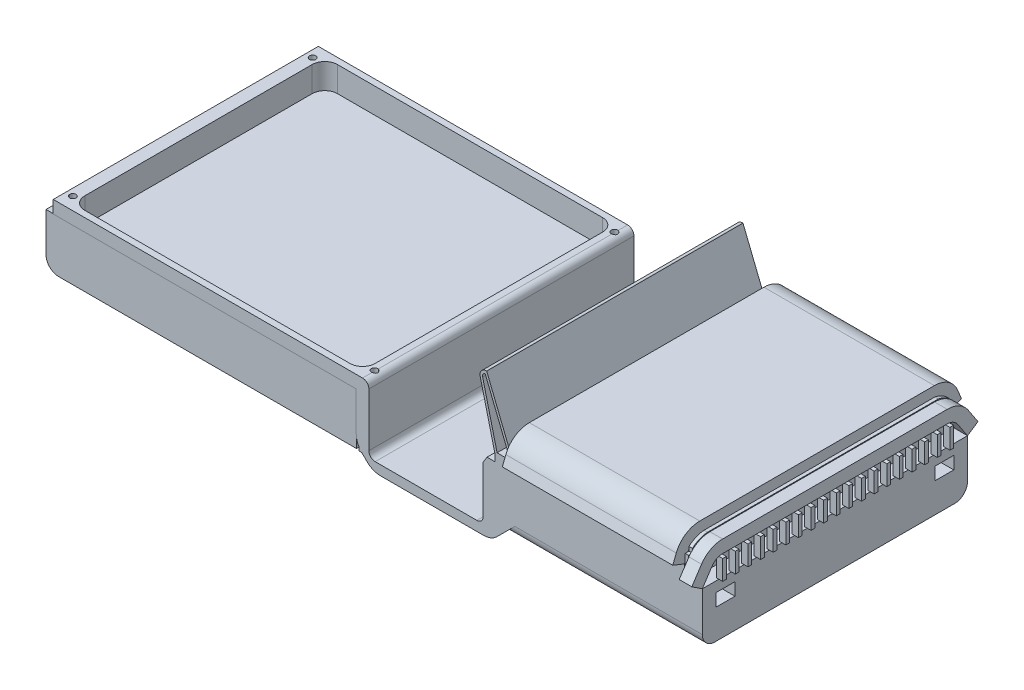
SolidWorks part; units mm, degrees
ref_plane "Front Plane" through (0, 0, 0) normal (0, 0, 1) x (1, 0, 0)
ref_plane "Top Plane" through (0, 0, 0) normal (0, 1, 0) x (1, 0, 0)
ref_plane "Right Plane" through (0, 0, 0) normal (1, 0, 0) x (0, 0, -1)
sketch "Sketch1" plane through (0, 0, 0) normal (0, 0, 1) x (1, 0, 0)
  line L0 (-144.6727, 0) -> (257.8658, 0) construction
  line L1 (-242.1342, 0) -> (7.8658, 0)
  line L2 (7.8658, 0) -> (7.8658, -40.8579)
  line L3 (9.3302, -44.3934) -> (13.4724, -48.5355)
  line L4 (17.0079, -50) -> (98.7236, -50)
  line L5 (102.2592, -48.5355) -> (106.4013, -44.3934)
  line L6 (107.8658, -40.8579) -> (107.8658, 0)
  line L7 (107.8658, 0) -> (257.8658, 0)
  arc A0 (106.4013, -44.3934) -> (107.8658, -40.8579) centre (102.8658, -40.8579) ccw
  arc A1 (98.7236, -50) -> (102.2592, -48.5355) centre (98.7236, -45) ccw
  arc A2 (13.4724, -48.5355) -> (17.0079, -50) centre (17.0079, -45) ccw
  arc A3 (7.8658, -40.8579) -> (9.3302, -44.3934) centre (12.8658, -40.8579) ccw
  point P5 (121.9448, 0)
  point P12 (-135.7907, 0)
  point P13 (158.4975, 0)
  point P16 (107.8658, -42.9289)
  point P19 (100.7947, -50)
  point P22 (14.9368, -50)
  point P25 (7.8658, -42.9289)
  dimension "D7" = 5
  dimension "D1" = 250
  dimension "D2" = 100
  dimension "D3" = 150
  dimension "D4" = 50
  dimension "D5" = 10
  dimension "D6" = 10
extrude "Extrude-Thin1" add sketch "Sketch1" against normal mid plane 210 thin
sketch "Sketch3" plane through (257.8658, 0, 0) normal (1, 0, 0) x (0, 0, -1)
  line L0 (-105, 0) -> (-102.2142, 7.0316)
  line L1 (-92.9172, 13.3483) -> (92.9172, 13.3483)
  line L2 (0, -17.7197) -> (0, 27.8327) construction
  line L3 (105, 0) -> (102.2142, 7.0316)
  arc A0 (-102.2142, 7.0316) -> (-92.9172, 13.3483) centre (-92.9172, 3.3483) cw
  arc A1 (102.2142, 7.0316) -> (92.9172, 13.3483) centre (92.9172, 3.3483) ccw
  point P13 (0, 13.3483)
  dimension "D1" = 10
extrude "Extrude-Thin2" add sketch "Sketch3" against normal blind 135 separate body thin thin type one direction wall 10
sketch "Sketch4" plane through (0, 0, 0) normal (1, 0, 0) x (0, 0, -1)
  line L0 (105, -51.4645) -> (105, -40.8579) construction
  line L1 (-105, -10) -> (105, -10)
  line L2 (-105, -10) -> (-105, -51.4645)
  line L3 (-105, -51.4645) -> (105, -51.4645)
  line L4 (105, -10) -> (105, -51.4645)
extrude "Boss-Extrude1" add sketch "Sketch4" along normal blind 272
sketch "Sketch5" plane through (0, 0, 105) normal (0, 0, 1) x (1, 0, 0)
  line L1 (7.8658, -10) -> (107.309, -10)
  line L2 (7.8658, -10) -> (7.8658, -52.3732)
  line L3 (7.8658, -52.3732) -> (107.309, -52.3732)
  line L4 (107.309, -10) -> (107.309, -52.3732)
extrude "Cut-Extrude1" cut sketch "Sketch5" against normal blind 709
sketch "Sketch6" plane through (272, 0, 0) normal (1, 0, 0) x (0, 0, -1)
  line L0 (0, -68.2544) -> (0, 40.5144) construction
  line L1 (79.1444, -18.0373) -> (79.1444, -28.0373)
  line L2 (-94.1444, -18.0373) -> (-79.1444, -18.0373)
  line L3 (-94.1444, -18.0373) -> (-94.1444, -28.0373)
  line L4 (-94.1444, -28.0373) -> (-79.1444, -28.0373)
  line L5 (-79.1444, -18.0373) -> (-79.1444, -28.0373)
  line L6 (94.1444, -18.0373) -> (79.1444, -18.0373)
  line L7 (94.1444, -18.0373) -> (94.1444, -28.0373)
  line L8 (94.1444, -28.0373) -> (79.1444, -28.0373)
  dimension "D1" = 15
  dimension "D2" = 10
extrude "Cut-Extrude3" cut sketch "Sketch6" against normal blind 10 contours L3 L2 L5 L4 | L1 L8 L7 L6
sketch "Sketch9" plane through (0, 0, 105) normal (0, 0, 1) x (1, 0, 0)
  line L0 (107.8658, 0) -> (96.0485, 47.7155)
  line L1 (100.9018, 53.9175) -> (101.1891, 53.9175)
  line L2 (101.1891, 53.9175) -> (122.8658, 0)
  line L3 (122.8658, 0) -> (107.8658, 0)
  line L4 (99.906, 51.7474) -> (99.906, 51.7474)
  line L5 (99.906, 51.7474) -> (119.9061, 2)
  line L6 (119.9061, 2) -> (109.4309, 2)
  line L7 (109.4309, 2) -> (97.9898, 48.1963)
  arc A0 (96.0485, 47.7155) -> (100.9018, 53.9175) centre (100.9018, 48.9175) cw
  arc A1 (97.9898, 48.1963) -> (99.906, 51.7474) centre (100.9018, 48.9175) cw
  dimension "D1" = 5
  dimension "D2" = 2
extrude "Boss-Extrude12" add sketch "Sketch9" against normal blind 203
sketch "Sketch10" plane through (272, 0, 0) normal (1, 0, 0) x (0, 0, -1)
  line L0 (-105, -10) -> (-97.301, 1.6328)
  line L1 (-88.9619, 6.1138) -> (88.9619, 6.1138)
  line L2 (0, -30.3296) -> (0, 35.3529) construction
  line L3 (105, -10) -> (97.301, 1.6328)
  arc A0 (-97.301, 1.6328) -> (-88.9619, 6.1138) centre (-88.9619, -3.8862) cw
  arc A1 (97.301, 1.6328) -> (88.9619, 6.1138) centre (88.9619, -3.8862) ccw
  point P10 (0, 6.1138)
  dimension "D1" = 10
extrude "Extrude-Thin4" add sketch "Sketch10" against normal blind 10 separate body thin thin type one direction wall 10
sketch "Sketch11" plane through (272, 0, 0) normal (1, 0, 0) x (0, 0, -1)
  line L0 (105, -10) -> (-105, -10) construction
  line L1 (-91.9035, 5.6713) -> (-88.9619, 5.6713)
  line L2 (-91.9035, 5.6713) -> (-91.9035, -10)
  line L3 (-91.9035, -10) -> (-88.9619, -10)
  line L4 (-88.9619, 5.6713) -> (-88.9619, -10)
  line L5 (-81.9035, 5.6713) -> (-81.9035, -10)
  line L6 (-81.9035, 5.6713) -> (-78.9619, 5.6713)
  line L7 (-78.9619, 5.6713) -> (-78.9619, -10)
  line L8 (-81.9035, -10) -> (-78.9619, -10)
  line L9 (-71.9035, 5.6713) -> (-71.9035, -10)
  line L10 (-71.9035, 5.6713) -> (-68.9619, 5.6713)
  line L11 (-68.9619, 5.6713) -> (-68.9619, -10)
  line L12 (-71.9035, -10) -> (-68.9619, -10)
  line L13 (-61.9035, 5.6713) -> (-61.9035, -10)
  line L14 (-61.9035, 5.6713) -> (-58.9619, 5.6713)
  line L15 (-58.9619, 5.6713) -> (-58.9619, -10)
  line L16 (-61.9035, -10) -> (-58.9619, -10)
  line L17 (-51.9035, 5.6713) -> (-51.9035, -10)
  line L18 (-51.9035, 5.6713) -> (-48.9619, 5.6713)
  line L19 (-48.9619, 5.6713) -> (-48.9619, -10)
  line L20 (-51.9035, -10) -> (-48.9619, -10)
  line L21 (-41.9035, 5.6713) -> (-41.9035, -10)
  line L22 (-41.9035, 5.6713) -> (-38.9619, 5.6713)
  line L23 (-38.9619, 5.6713) -> (-38.9619, -10)
  line L24 (-41.9035, -10) -> (-38.9619, -10)
  line L25 (-31.9035, 5.6713) -> (-31.9035, -10)
  line L26 (-31.9035, 5.6713) -> (-28.9619, 5.6713)
  line L27 (-28.9619, 5.6713) -> (-28.9619, -10)
  line L28 (-31.9035, -10) -> (-28.9619, -10)
  line L29 (-21.9035, 5.6713) -> (-21.9035, -10)
  line L30 (-21.9035, 5.6713) -> (-18.9619, 5.6713)
  line L31 (-18.9619, 5.6713) -> (-18.9619, -10)
  line L32 (-21.9035, -10) -> (-18.9619, -10)
  line L33 (-11.9035, 5.6713) -> (-11.9035, -10)
  line L34 (-11.9035, 5.6713) -> (-8.9619, 5.6713)
  line L35 (-8.9619, 5.6713) -> (-8.9619, -10)
  line L36 (-11.9035, -10) -> (-8.9619, -10)
  line L37 (-1.9035, 5.6713) -> (-1.9035, -10)
  line L38 (-1.9035, 5.6713) -> (1.0381, 5.6713)
  line L39 (1.0381, 5.6713) -> (1.0381, -10)
  line L40 (-1.9035, -10) -> (1.0381, -10)
  line L41 (8.0965, 5.6713) -> (8.0965, -10)
  line L42 (8.0965, 5.6713) -> (11.0381, 5.6713)
  line L43 (11.0381, 5.6713) -> (11.0381, -10)
  line L44 (8.0965, -10) -> (11.0381, -10)
  line L45 (18.0965, 5.6713) -> (18.0965, -10)
  line L46 (18.0965, 5.6713) -> (21.0381, 5.6713)
  line L47 (21.0381, 5.6713) -> (21.0381, -10)
  line L48 (18.0965, -10) -> (21.0381, -10)
  line L49 (28.0965, 5.6713) -> (28.0965, -10)
  line L50 (28.0965, 5.6713) -> (31.0381, 5.6713)
  line L51 (31.0381, 5.6713) -> (31.0381, -10)
  line L52 (28.0965, -10) -> (31.0381, -10)
  line L53 (38.0965, 5.6713) -> (38.0965, -10)
  line L54 (38.0965, 5.6713) -> (41.0381, 5.6713)
  line L55 (41.0381, 5.6713) -> (41.0381, -10)
  line L56 (38.0965, -10) -> (41.0381, -10)
  line L57 (48.0965, 5.6713) -> (48.0965, -10)
  line L58 (48.0965, 5.6713) -> (51.0381, 5.6713)
  line L59 (51.0381, 5.6713) -> (51.0381, -10)
  line L60 (48.0965, -10) -> (51.0381, -10)
  line L61 (58.0965, 5.6713) -> (58.0965, -10)
  line L62 (58.0965, 5.6713) -> (61.0381, 5.6713)
  line L63 (61.0381, 5.6713) -> (61.0381, -10)
  line L64 (58.0965, -10) -> (61.0381, -10)
  line L65 (68.0965, 5.6713) -> (68.0965, -10)
  line L66 (68.0965, 5.6713) -> (71.0381, 5.6713)
  line L67 (71.0381, 5.6713) -> (71.0381, -10)
  line L68 (68.0965, -10) -> (71.0381, -10)
  line L69 (78.0965, 5.6713) -> (78.0965, -10)
  line L70 (78.0965, 5.6713) -> (81.0381, 5.6713)
  line L71 (81.0381, 5.6713) -> (81.0381, -10)
  line L72 (78.0965, -10) -> (81.0381, -10)
  line L73 (88.0965, 5.6713) -> (88.0965, -10)
  line L74 (88.0965, 5.6713) -> (91.0381, 5.6713)
  line L75 (91.0381, 5.6713) -> (91.0381, -10)
  line L76 (88.0965, -10) -> (91.0381, -10)
  arc A0 (-88.9619, 6.1138) -> (-97.301, 1.6328) centre (-88.9619, -3.8862) ccw construction
  dimension "D1" = 19
extrude "Boss-Extrude13" add sketch "Sketch11" along normal blind 3 and the other way blind 2
sketch "Sketch12" plane through (0, 0, 105) normal (0, 0, 1) x (1, 0, 0)
  line L0 (258.4199, -10) -> (261.1323, -10)
  line L1 (272, -10) -> (257.8658, -10) construction
  line L2 (261.1323, -10) -> (261.1323, 15.8877)
  line L3 (261.1323, 15.8877) -> (258.4199, 15.8877)
  line L4 (258.4199, 15.8877) -> (258.4199, -10)
extrude "Boss-Extrude16" add sketch "Sketch12" against normal blind 210
sketch "Sketch13" plane through (261.1323, 0, 0) normal (1, 0, 0) x (0, 0, -1)
  line L0 (-104.85, 15.8877) -> (-105, 7.4673)
  line L1 (105, 15.8877) -> (-105, 15.8877) construction
  line L2 (-105, -10) -> (-105, 15.8877) construction
  line L3 (-104.85, 15.8877) -> (-90.0443, 15.8877)
  arc A0 (-105, 7.4673) -> (-90.0443, 15.8877) centre (-88.4127, -4.502) cw
extrude "Cut-Extrude5" cut sketch "Sketch13" against normal blind 3 contours A0 L3 L0
sketch "Sketch14" plane through (0, 0, 105) normal (0, 0, 1) x (1, 0, 0)
  line L0 (258.4199, 7.4673) -> (261.1323, 7.4673) construction
  line L1 (258.4199, 15.8877) -> (261.1323, 15.8877)
  line L2 (258.4199, 15.8877) -> (258.4199, 7.4673)
  line L3 (258.4199, 7.4673) -> (261.1323, 7.4673)
  line L4 (261.1323, 15.8877) -> (261.1323, 7.4673)
  line L5 (261.1323, 7.4673) -> (261.1323, 15.8877) construction
extrude "Cut-Extrude6" cut sketch "Sketch14" against normal blind 3
sketch "Sketch15" plane through (261.1323, 0, 0) normal (1, 0, 0) x (0, 0, -1)
  line L0 (105, 15.8877) -> (92.7242, 15.8877)
  line L1 (105, 15.8877) -> (-90.0443, 15.8877) construction
  line L2 (105, 15.8877) -> (104.921, 8.1681)
  arc A0 (105.64, 7.1519) -> (88.9619, 16.1138) centre (88.9619, -3.8862) ccw construction
  arc A1 (92.7242, 15.8877) -> (104.921, 8.1681) centre (88.7356, -3.9094) cw
extrude "Cut-Extrude7" cut sketch "Sketch15" against normal blind 3
sketch "Sketch16" plane through (0, 0, -105) normal (0, 0, -1) x (-1, 0, 0)
  line L0 (-258.4199, 15.8877) -> (-258.4199, -10) construction
  line L1 (-261.1323, 15.8877) -> (-258.4199, 15.8877)
  line L2 (-261.1323, 15.8877) -> (-261.1323, 5.5097)
  line L3 (-261.1323, 5.5097) -> (-258.4199, 5.5097)
  line L4 (-258.4199, 15.8877) -> (-258.4199, 5.5097)
extrude "Cut-Extrude8" cut sketch "Sketch16" against normal blind 3
sketch "Sketch19" plane through (0, 0, 105) normal (0, 0, 1) x (1, 0, 0)
  line L0 (107.8658, -5) -> (101.4461, -5)
  line L1 (107.8658, -10) -> (107.8658, 0) construction
  line L2 (101.4461, -5) -> (98.3592, -10)
  line L3 (98.3592, -10) -> (98.3592, -52.3732)
  line L4 (7.8658, -52.3732) -> (107.309, -52.3732) construction
  line L5 (98.3592, -52.3732) -> (107.309, -52.3732)
  line L6 (107.309, -52.3732) -> (107.309, -10)
  line L8 (107.309, -10) -> (107.8658, -10)
  line L10 (107.8658, -5) -> (107.8658, -10)
extrude "Boss-Extrude17" add sketch "Sketch19" against normal blind 209
fillet "Fillet1" radius 10 1 edges at (192.7362, -51.4645, 105)
fillet "Fillet2" radius 10 1 edges at (192.7362, -51.4645, -105)
sketch "Sketch20" plane through (-2.1342, 0, 0) normal (-1, 0, 0) x (0, 0, 1)
  line L7 (-105, -10) -> (104.7274, -10)
  line L8 (-105, -10) -> (-105, -51.0601)
  line L9 (-105, -51.0601) -> (104.7274, -51.0601)
  line L10 (104.7274, -10) -> (104.7274, -51.0601)
extrude "Boss-Extrude18" add sketch "Sketch20" along normal blind 246
fillet "Fillet3" radius 10 1 edges at (-248.1342, -51.0601, -0.1363)
sketch "Sketch21" plane through (0, 0, 0) normal (0, 1, 0) x (1, 0, 0)
  line L0 (-242.1342, 105) -> (-242.1342, -105) construction
  line L1 (-222.1342, 100.1003) -> (-12.1342, 100.1003)
  line L2 (-232.1342, 90.1003) -> (-232.1342, -90)
  line L3 (-222.1342, -100) -> (-12.1342, -100)
  line L4 (-2.1342, 90.1003) -> (-2.1342, -90)
  line L5 (7.8658, 105) -> (7.8658, -105) construction
  line L6 (-242.1342, -105) -> (7.8658, -105) construction
  arc A0 (-232.1342, -90) -> (-222.1342, -100) centre (-222.1342, -90) ccw
  arc A1 (-12.1342, -100) -> (-2.1342, -90) centre (-12.1342, -90) ccw
  arc A2 (-12.1342, 100.1003) -> (-2.1342, 90.1003) centre (-12.1342, 90.1003) cw
  arc A3 (-222.1342, 100.1003) -> (-232.1342, 90.1003) centre (-222.1342, 90.1003) ccw
  dimension "D1" = 10
  dimension "D2" = 180.1003
  dimension "D3" = 10
  dimension "D4" = 10
  dimension "D5" = 5
extrude "Cut-Extrude9" cut sketch "Sketch21" against normal blind 20
fillet "Fillet4" radius 5 1 edges at (7.8658, 0, 0)
fillet "Fillet5" radius 5 1 edges at (7.8658, -52.3732, 0)
fillet "Fillet6" radius 5 1 edges at (98.3592, -52.3732, 0.5)
sketch "Sketch24" plane through (0, 0, 0) normal (0, 1, 0) x (1, 0, 0)
  line L1 (-242.1342, 105) -> (-242.1342, -104.7274) construction
  line L2 (-264.0977, 0) -> (2.8658, 0) construction
  line L3 (2.8658, -105) -> (2.8658, 105) construction
  line L4 (7.8658, 105) -> (7.8658, -105) construction
  line L5 (-242.1342, 105) -> (2.8658, 105) construction
  circle A0 centre (-236.6342, -95) radius 2.5
  circle A1 centre (-236.6342, 95) radius 2.5
  circle A2 centre (2.3658, 95) radius 2.5
  circle A4 centre (2.3658, -95) radius 2.5
  dimension "D2" = 5
  dimension "D5" = 5
  dimension "D6" = 10
  dimension "D3" = 5.5
  dimension "D4" = 5.5
extrude "Cut-Extrude12" cut sketch "Sketch24" against normal blind 15
